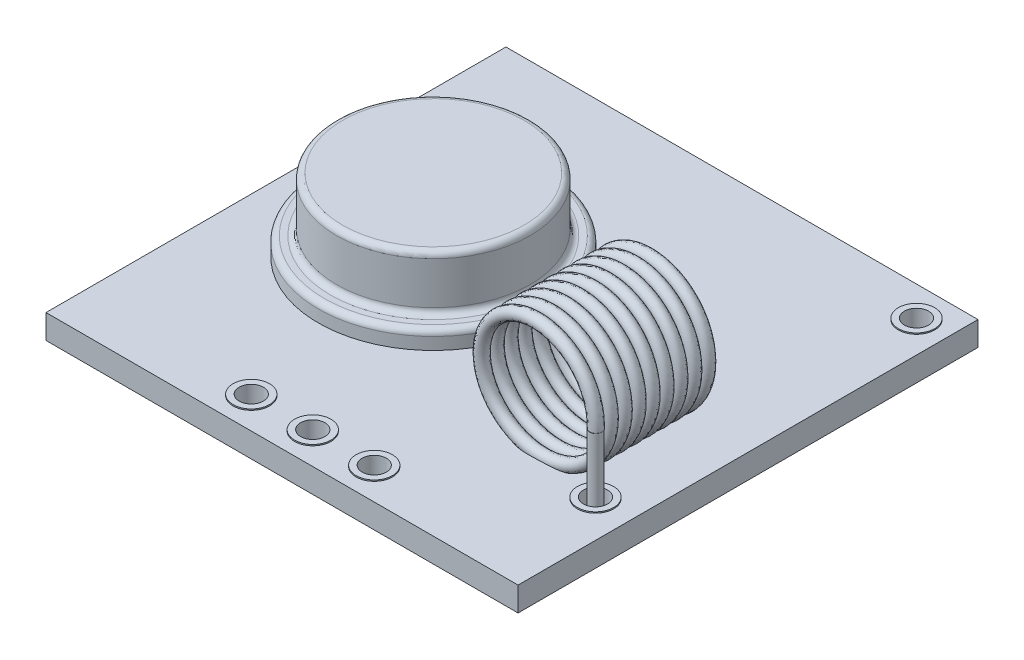
SolidWorks part; units mm, degrees
ref_plane "Front Plane" through (0, 0, 0) normal (0, 0, 1) x (1, 0, 0)
ref_plane "Top Plane" through (0, 0, 0) normal (0, 1, 0) x (1, 0, 0)
ref_plane "Right Plane" through (0, 0, 0) normal (1, 0, 0) x (0, 0, -1)
sketch "Sketch1" plane through (0, 0, 0) normal (0, 1, 0) x (1, 0, 0)
  line L0 (9.75, 1.27) -> (7.21, 1.27)
  line L1 (0, 0) -> (19.5, 0)
  line L2 (0, 0) -> (0, 19)
  line L3 (0, 19) -> (19.5, 19)
  line L4 (19.5, 0) -> (19.5, 19)
  line L5 (9.75, 1.27) -> (12.29, 1.27)
  circle A0 centre (7.21, 1.27) radius 0.5
  circle A1 centre (9.75, 1.27) radius 0.5
  circle A2 centre (12.29, 1.27) radius 0.5
  circle A3 centre (18.23, 17.73) radius 0.5
  circle A4 centre (18, 4.7) radius 0.5
  circle A5 centre (13, 9.6) radius 0.5
  dimension "D7" = 1
  dimension "D1" = 19.5
  dimension "D2" = 19
  dimension "D3" = 2.54
  dimension "D4" = 2.54
  dimension "D5" = 9.75
  dimension "D6" = 1.27
  dimension "D8" = 1.27
  dimension "D9" = 1.27
  dimension "D10" = 4.7
  dimension "D11" = 9.6
  dimension "D12" = 6.5
  dimension "D13" = 1.5
extrude "Boss-Extrude1" add sketch "Sketch1" along normal blind 1
ref_plane "Plane1" through (0, 0.5, 0) normal (0, 1, 0) x (1, 0, 0)
sketch "Sketch2" plane through (0, 1, 0) normal (0, 1, 0) x (1, 0, 0)
  circle A0 centre (7.21, 1.27) radius 0.5 construction
  circle A1 centre (7.21, 1.27) radius 0.5
  circle A2 centre (12.29, 1.27) radius 0.5 construction
  circle A3 centre (12.29, 1.27) radius 0.5
  circle A4 centre (18.23, 17.73) radius 0.5 construction
  circle A5 centre (18.23, 17.73) radius 0.5
  circle A6 centre (9.75, 1.27) radius 0.5 construction
  circle A7 centre (9.75, 1.27) radius 0.5
  circle A8 centre (18.23, 17.73) radius 0.75
  circle A9 centre (12.29, 1.27) radius 0.75
  circle A10 centre (9.75, 1.27) radius 0.75
  circle A11 centre (7.21, 1.27) radius 0.75
  circle A12 centre (13, 9.6) radius 0.5 construction
  circle A13 centre (18, 4.7) radius 0.5
  circle A14 centre (18, 4.7) radius 0.5
  circle A15 centre (13, 9.6) radius 0.5
  circle A16 centre (13, 9.6) radius 0.75
  circle A17 centre (18, 4.7) radius 0.75
  dimension "D1" = 1.5
  dimension "D2" = 0
extrude "Boss-Extrude2" add sketch "Sketch2" along normal blind 0.05
mirror "Mirror1" about plane through (0, 0.5, 0) normal (0, 1, 0) of "Boss-Extrude2"
sketch "Sketch4" plane through (0, 1, 0) normal (0, 1, 0) x (1, 0, 0)
  line L0 (0, 9.5) -> (6.5, 9.5)
  line L4 (0, 0) -> (19.5, 0)
  line L5 (19.5, 0) -> (19.5, 19)
  line L6 (19.5, 19) -> (0, 19)
  line L7 (0, 19) -> (0, 0)
  line L8 (0, 0) -> (19.5, 0)
  line L9 (19.5, 0) -> (19.5, 19)
  line L10 (19.5, 19) -> (0, 19)
  line L11 (0, 19) -> (0, 0)
  dimension "D2" = 6.5
  dimension "D3" = 9.5
  dimension "D1" = 0
ref_plane "Plane2" through (6.5, 0, 0) normal (-1, 0, 0) x (0, 0, 1)
sketch "Sketch5" plane through (6.5, 0, 0) normal (-1, 0, 0) x (0, 0, 1)
  line L0 (-9.5, 1) -> (-9.5, 4.5)
  line L1 (-9.5, 4.5) -> (-13.25, 4.5)
  line L2 (-13.5, 4.25) -> (-13.5, 2.5)
  line L3 (-13.75, 2.25) -> (-14, 2.25)
  line L4 (-14.25, 2) -> (-14.25, 1.5)
  line L5 (-14.25, 1.5) -> (-9.5, 1.5)
  arc A0 (-13.75, 2.25) -> (-13.5, 2.5) centre (-13.75, 2.5) ccw
  arc A1 (-13.5, 4.25) -> (-13.25, 4.5) centre (-13.25, 4.25) cw
  arc A2 (-14.25, 2) -> (-14, 2.25) centre (-14, 2) cw
  point P12 (-13.5, 4.5)
  dimension "D6" = 0.25
  dimension "D1" = 3.5
  dimension "D2" = 0.5
  dimension "D3" = 4.75
  dimension "D4" = 4
  dimension "D5" = 0.75
revolve "Revolve1" add sketch "Sketch5" angle 360 about L0
ref_plane "Plane3" through (0, 0, -9.6) normal (0, 0, 1) x (1, 0, 0)
sketch "Sketch8" plane through (0, 0, -9.6) normal (0, 0, 1) x (1, 0, 0)
  line L0 (0, 1) -> (19.5, 1) construction
  line L1 (0, 1) -> (19.5, 1)
  line L2 (13.5, 1.05) -> (12.5, 1.05) construction
  line L3 (13.5, 1.05) -> (12.5, 1.05)
  line L4 (13, 1.05) -> (13, 6.9648)
sketch "Sketch10" plane through (0, 0, -9.6) normal (0, 0, 1) x (1, 0, 0)
  line L0 (0, 1) -> (19.5, 1) construction
  line L1 (13, 1.05) -> (13, 6.9648) construction
  circle A0 centre (15.5, 3.5) radius 2.5
  dimension "D1" = 5
curve "Helix/Spiral1" pitch 0.575 height 4.8875 turns 8.5
sketch "Sketch12" plane through (0, 0.5, 0) normal (0, 1, 0) x (1, 0, 0)
  circle A0 centre (13, 9.6) radius 0.5 construction
  circle A1 centre (18, 4.7) radius 0.5 construction
  circle A2 centre (13, 9.6) radius 0.5
  circle A3 centre (18, 4.7) radius 0.5
  circle A4 centre (18, 4.7) radius 0.2528
  circle A5 centre (13, 9.6) radius 0.7427
  circle A6 centre (13, 9.6) radius 0.2528
extrude "Boss-Extrude3" add sketch "Sketch12" along normal up to vertex (3 mm away) separate body contours A6 | A4
sketch "Sketch13" plane through (0, 3.5, 0) normal (0, 1, 0) x (1, 0, 0)
  circle A1 centre (13, 9.6) radius 0.2528
  circle A2 centre (13, 9.6) radius 0.2528
  dimension "D1" = 0
sweep "Sweep1" add profiles "Sketch13" path "Helix/Spiral1"
sketch "Sketch14" plane through (0, 1, 0) normal (0, 1, 0) x (1, 0, 0)
  line L0 (6.5, 9.5) -> (6.5, 11)
  line L1 (6.5, 9.5) -> (6.5, 8)
  circle A0 centre (6.5, 11) radius 0.5
  circle A1 centre (6.5, 8) radius 0.5
  dimension "D2" = 1
  dimension "D1" = 1.5
extrude "Boss-Extrude4" add sketch "Sketch14" along normal up to surface (0.5 mm away) contours A0 | A1 up to face at (6.5, 1.5, -14.25)
equation "\"D4@Sketch1\"=\"D3@Sketch1\""
equation "\"D5@Sketch1\"=\"D1@Sketch1\"/2"
equation "\"D8@Sketch1\"=\"D6@Sketch1\""
equation "\"D9@Sketch1\"=\"D6@Sketch1\""
